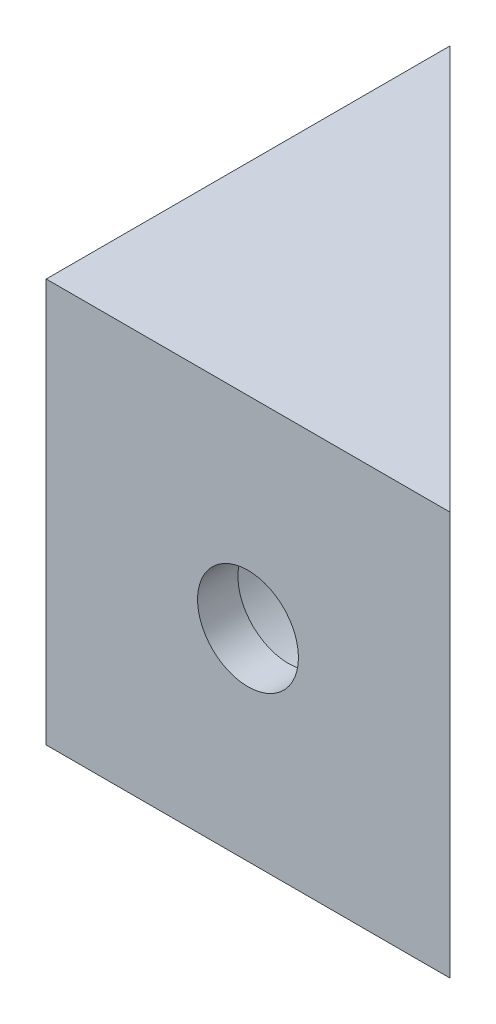
SolidWorks part; units mm, degrees
ref_plane "Front Plane" through (0, 0, 0) normal (0, 0, 1) x (1, 0, 0)
ref_plane "Top Plane" through (0, 0, 0) normal (0, 1, 0) x (1, 0, 0)
ref_plane "Right Plane" through (0, 0, 0) normal (1, 0, 0) x (0, 0, -1)
sketch "Sketch1" plane through (0, 0, 0) normal (0, 1, 0) x (1, 0, 0)
  line L0 (0, 0) -> (0, 20)
  line L1 (0, 20) -> (20, 0)
  line L2 (20, 0) -> (0, 0)
  dimension "D1" = 20
  dimension "D2" = 20
extrude "Boss-Extrude1" add sketch "Sketch1" along normal blind 20
sketch "Sketch2" plane through (0, 0, 0) normal (0, 0, 1) x (1, 0, 0)
  line L0 (0, 20) -> (20, 0) construction
  circle A0 centre (10, 10) radius 2.5
  dimension "D1" = 5
extrude "Cut-Extrude1" cut sketch "Sketch2" against normal through all
sketch "Sketch3" plane through (0, 0, 0) normal (-1, 0, 0) x (0, 0, 1)
  line L0 (-20, 20) -> (0, 0) construction
  circle A0 centre (-10, 10) radius 2.5
  dimension "D1" = 5
extrude "Cut-Extrude2" cut sketch "Sketch3" against normal through all contours A0
sketch "Sketch4" plane through (0, 0, 0) normal (-1, 0, 0) x (0, 0, 1)
  circle A0 centre (-10, 10) radius 5
  dimension "D1" = 10
extrude "Cut-Extrude3" cut sketch "Sketch4" against normal through all from offset 2 contours A0 offset against normal yes
sketch "Sketch5" plane through (0, 0, 0) normal (0, 0, 1) x (1, 0, 0)
  circle A0 centre (10, 10) radius 5
  dimension "D1" = 10
extrude "Cut-Extrude4" cut sketch "Sketch5" against normal blind 20 from offset 2
